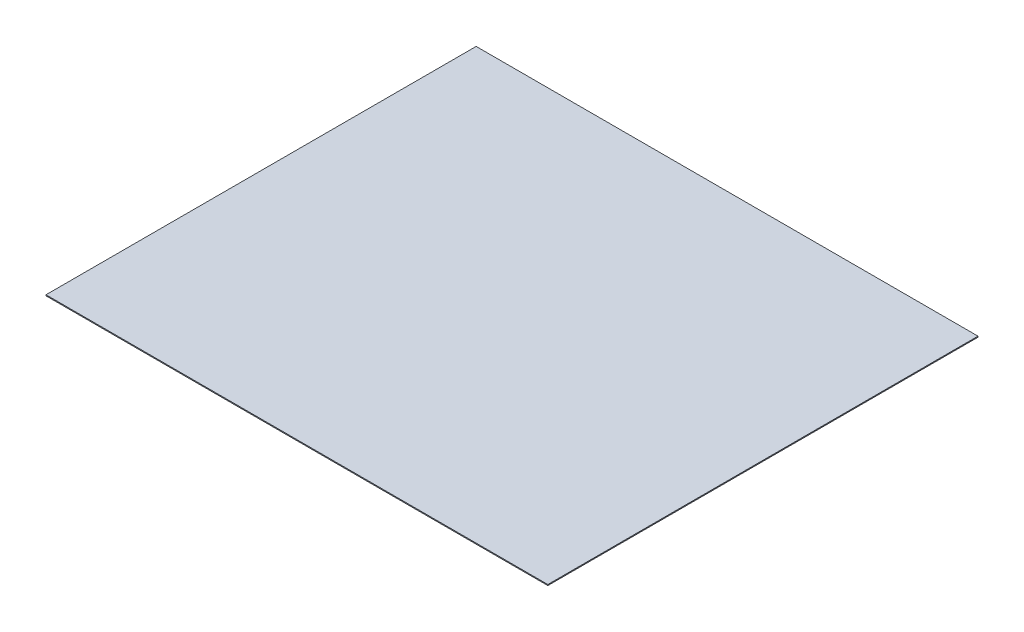
SolidWorks part; units mm, degrees
ref_plane "Front Plane" through (0, 0, 0) normal (0, 0, 1) x (1, 0, 0)
ref_plane "Top Plane" through (0, 0, 0) normal (0, 1, 0) x (1, 0, 0)
ref_plane "Right Plane" through (0, 0, 0) normal (1, 0, 0) x (0, 0, -1)
sketch "Sketch1" plane through (0, 0, 0) normal (0, 1, 0) x (1, 0, 0)
  line L1 (-133.35, 114.3) -> (133.35, 114.3)
  line L2 (-133.35, 114.3) -> (-133.35, -114.3)
  line L3 (-133.35, -114.3) -> (133.35, -114.3)
  line L4 (133.35, 114.3) -> (133.35, -114.3)
  line L5 (-133.35, 114.3) -> (133.35, -114.3) construction
  line L6 (-133.35, -114.3) -> (133.35, 114.3) construction
  point P0 (0, 0)
  dimension "D1" = 266.7
  dimension "D2" = 228.6
extrude "Boss-Extrude1" add sketch "Sketch1" along normal blind 0.508
